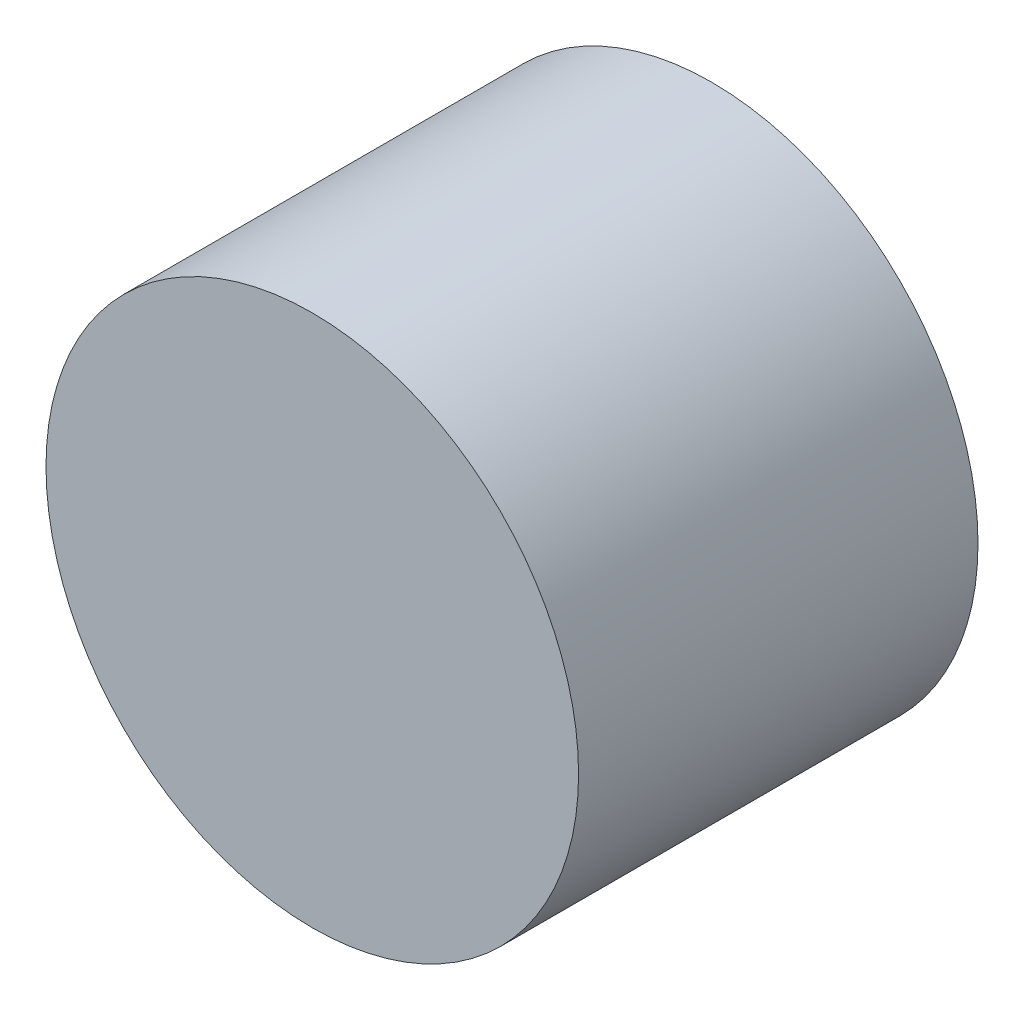
SolidWorks part; units mm, degrees
ref_plane "正面(Front)" through (0, 0, 0) normal (0, 0, 1) x (1, 0, 0)
ref_plane "平面(Top)" through (0, 0, 0) normal (0, 1, 0) x (1, 0, 0)
ref_plane "右側面(Right)" through (0, 0, 0) normal (1, 0, 0) x (0, 0, -1)
sketch "ｽｹｯﾁ1" plane through (0, 0, 0) normal (0, 0, 1) x (1, 0, 0)
  circle A0 centre (0, 0) radius 10
  dimension "D1" = 20
extrude "ﾎﾞｽ - 押し出し1" add sketch "ｽｹｯﾁ1" along normal blind 15
